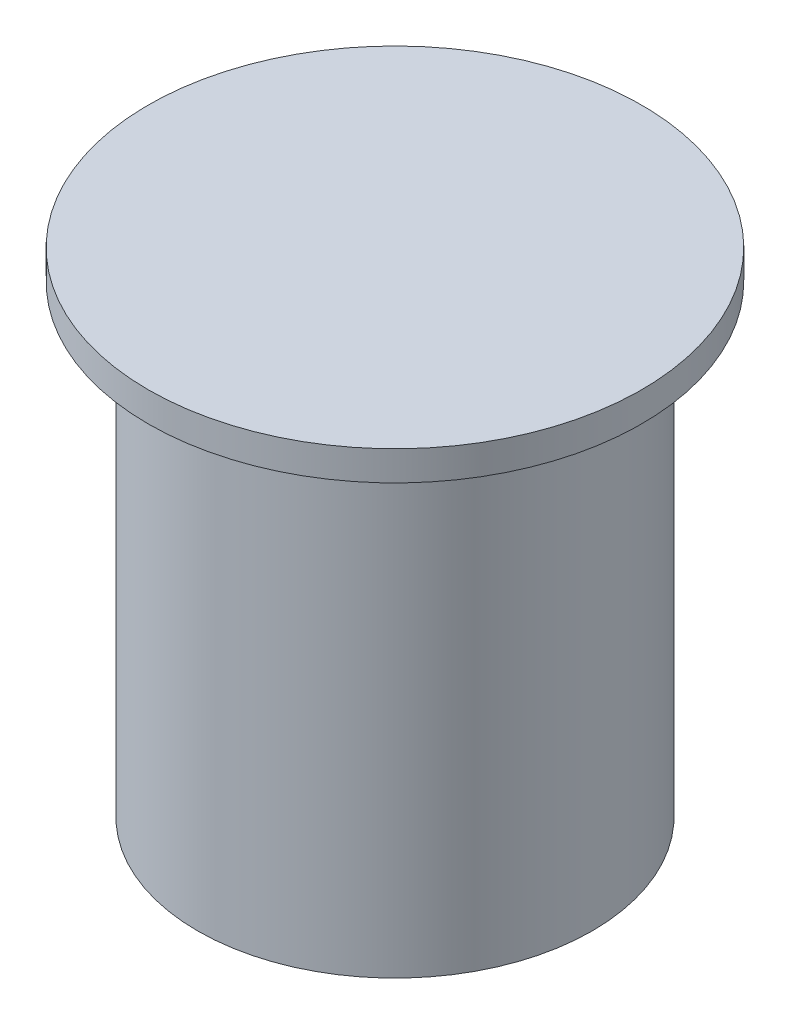
SolidWorks part; units mm, degrees
ref_plane "Спереди" through (0, 0, 0) normal (0, 0, 1) x (1, 0, 0)
ref_plane "Сверху" through (0, 0, 0) normal (0, 1, 0) x (1, 0, 0)
ref_plane "Справа" through (0, 0, 0) normal (1, 0, 0) x (0, 0, -1)
sketch "Эскиз1" plane through (0, 0, 0) normal (0, 1, 0) x (1, 0, 0)
  circle A0 centre (0, 0) radius 80
extrude "Бобышка-Вытянуть1" add sketch "Эскиз1" along normal blind 188
sketch "Эскиз2" plane through (0, 188, 0) normal (0, 1, 0) x (1, 0, 0)
  circle A0 centre (0, 0) radius 100
extrude "Бобышка-Вытянуть2" add sketch "Эскиз2" along normal blind 12
